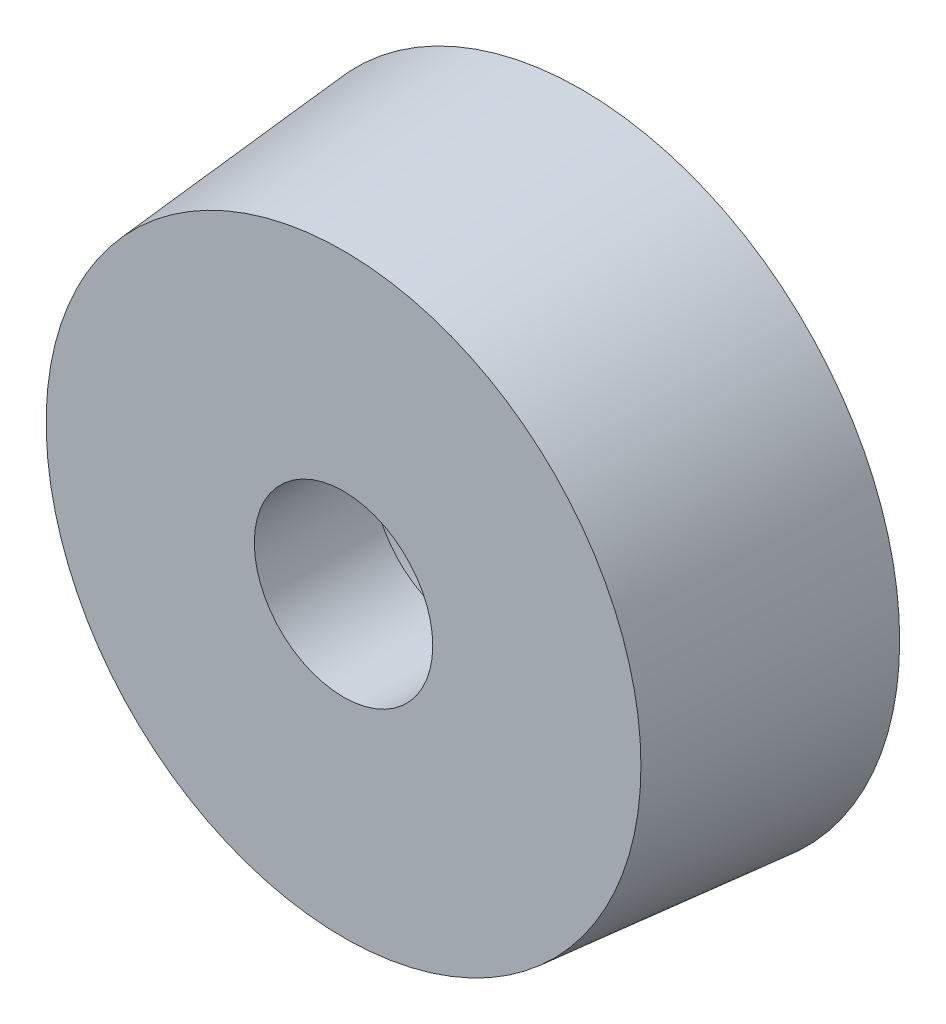
SolidWorks part; units mm, degrees
ref_plane "前视基准面" through (0, 0, 0) normal (0, 0, 1) x (1, 0, 0)
ref_plane "上视基准面" through (0, 0, 0) normal (0, 1, 0) x (1, 0, 0)
ref_plane "右视基准面" through (0, 0, 0) normal (1, 0, 0) x (0, 0, -1)
sketch "草图1" plane through (0, 0, 0) normal (0, 0, 1) x (1, 0, 0)
  circle A0 centre (0, 0) radius 10
  circle A1 centre (0, 0) radius 3
  dimension "D1" = 20
  dimension "D2" = 6
extrude "凸台-拉伸1" add sketch "草图1" along normal blind 8
cosmetic thread "装饰螺纹线1" parameters "D2"=18
draft "拔模1" type of draft neutral plane draft angle 5 faces to draft 1 face at (10, 0, 8) neutral plane through (0, 0, 8) neutral plane normal (0, 0, 1) parameters "D1"=5
sketch "草图2" plane through (0, 0, 0) normal (0, 0, -1) x (-1, 0, 0)
  circle A0 centre (0, 0) radius 6
  dimension "D1" = 12
extrude "切除-拉伸1" cut sketch "草图2" against normal blind 4
